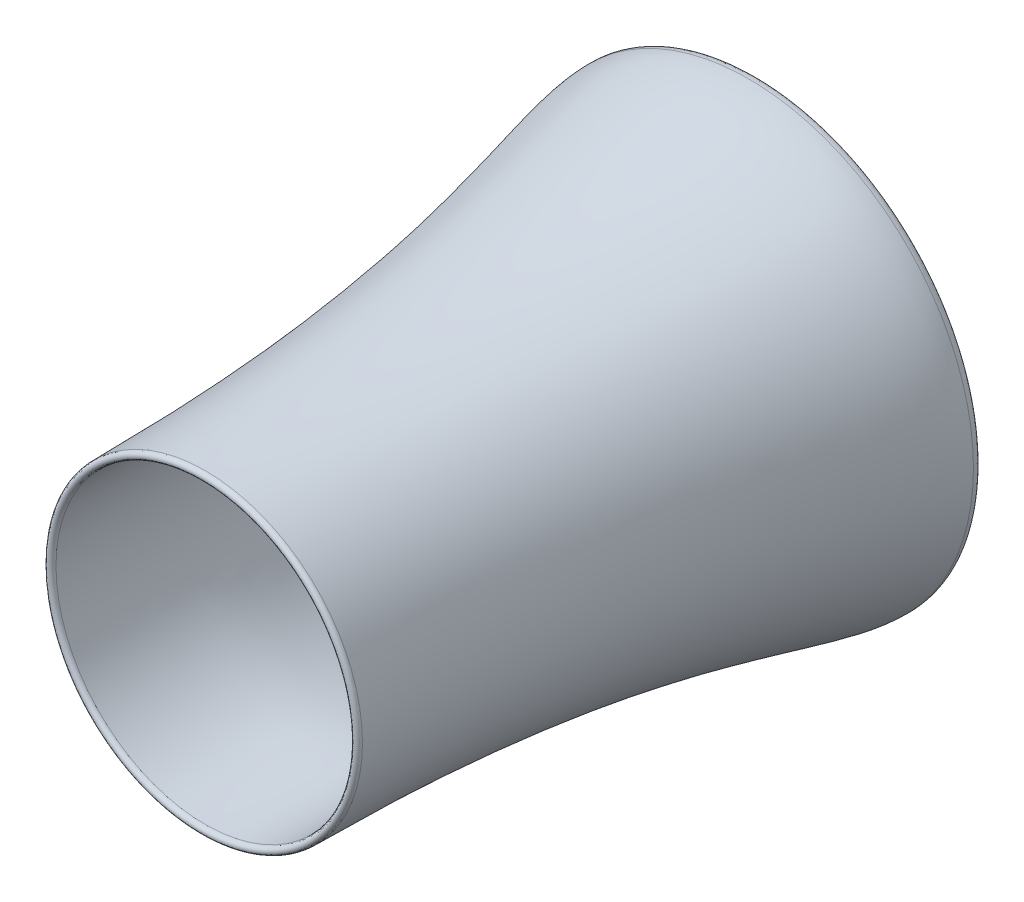
SolidWorks part; units mm, degrees
ref_plane "Front Plane" through (0, 0, 0) normal (0, 0, 1) x (1, 0, 0)
ref_plane "Top Plane" through (0, 0, 0) normal (0, 1, 0) x (1, 0, 0)
ref_plane "Right Plane" through (0, 0, 0) normal (1, 0, 0) x (0, 0, -1)
sketch "Sketch1" plane through (0, 0, 0) normal (0, 0, 1) x (1, 0, 0)
  circle A0 centre (0, 0) radius 50.8
  dimension "D1" = 101.6
ref_plane "Plane1" through (0, -254, 0) normal (0, 1, 0) x (1, 0, 0)
sketch "Sketch6" plane through (0, 0, 0) normal (0, 1, 0) x (1, 0, 0)
  line L0 (0, -99.6848) -> (0, 145.6048) construction
ref_plane "Plane2" through (0, -114.3, 0) normal (0, 1, 0) x (1, 0, 0)
sketch "Sketch12" plane through (0, 0, 0) normal (0, 1, 0) x (1, 0, 0)
  line L0 (0, -1104.7568) -> (0, -908.6135) construction
ref_plane "Plane3" through (0, 0, 203.2) normal (0, 0, 1) x (1, 0, 0)
ref_plane "Plane4" through (0, 0, 889) normal (0, 0, 1) x (1, 0, 0)
sketch "Sketch17" plane through (0, 0, 0) normal (0, 1, 0) x (1, 0, 0)
  line L0 (-259.4955, -43.5301) -> (-259.4955, 70.1436) construction
  line L1 (-110.6437, -1316.1124) -> (-110.6437, -853.5386) construction
  line L2 (-259.4955, 45.4622) -> (-387.328, 45.4622)
  line L3 (-387.328, 45.4622) -> (-387.328, -1084.8928)
  line L4 (-387.328, -1084.8928) -> (-110.6437, -1084.8928)
  spline S0 degree 3 poles (-259.4955, 45.4622) (-259.4955, -7.1736) (-207.7477, -105.8122) (-173.3147, -383.1384) (-92.4228, -818.9689) (-110.6437, -795.7842) (-110.6437, -1084.8928) knots 0 0 0 0 0.158009 0.206507 0.484977 1 1 1 1
sketch "Sketch21" plane through (0, 0, 0) normal (0, 1, 0) x (1, 0, 0)
  line L0 (-267.2369, -22.8536) -> (-267.2369, 113.778) construction
  line L1 (-126.7819, -1315.9117) -> (-126.7819, -853.874) construction
  line L2 (-259.4955, 45.4622) -> (-267.2369, 45.4622) construction
  line L3 (-110.6437, -1084.8928) -> (-126.7819, -1084.8928) construction
  line L4 (-110.6437, -1084.8928) -> (-126.7819, -1084.8928)
  line L6 (-259.4955, 45.4622) -> (-267.2369, 45.4622)
  spline S0 degree 3 poles (-259.4955, 45.4622) (-259.4955, -7.1736) (-207.7477, -105.8122) (-173.3147, -383.1384) (-92.4228, -818.9689) (-110.6437, -795.7842) (-110.6437, -1084.8928) knots 0 0 0 0 0.158009 0.206507 0.484977 1 1 1 1
  spline S1 degree 3 poles (-267.2369, 45.4622) (-267.2369, -79.9218) (-126.7819, -354.5837) (-126.7819, -1084.8928) knots 0 0 0 0 1 1 1 1
sketch "Sketch22" plane through (0, 0, 0) normal (0, 1, 0) x (1, 0, 0)
  line L0 (-267.2369, 45.4622) -> (-259.4955, 45.4622)
  line L1 (-259.4955, 41.6531) -> (-259.4955, 49.2713) construction
  line L2 (-267.2369, 46.8549) -> (-267.2369, 44.0695) construction
  spline S0 degree 3 poles (-267.2369, 45.4622) (-267.2369, 62.3955) (-259.4955, 62.3955) (-259.4955, 45.4622) knots 0 0 0 0 1 1 1 1
sketch "Sketch23" plane through (0, 0, 0) normal (0, 1, 0) x (1, 0, 0)
  line L0 (-126.7819, -1084.8928) -> (-110.6437, -1084.8928)
  line L1 (-126.7819, -1094.1039) -> (-126.7819, -1075.6818) construction
  line L2 (-110.6437, -1074.3198) -> (-110.6437, -1095.4658) construction
  spline S0 degree 3 poles (-126.7819, -1084.8928) (-126.7819, -1097.5928) (-110.6437, -1097.5928) (-110.6437, -1084.8928) knots 0 0 0 0 1 1 1 1
ref_plane "基准面1" through (200, 0, 0) normal (1, 0, 0) x (0, 0, -1)
ref_axis "基准轴1" through (200, 0, -115.7912) along (0, 0, 1)
revolve "旋转1" add sketch "Sketch21" angle 360 about axis through (200, 0, -115.7912) along (0, 0, 1)
revolve "旋转2" add sketch "Sketch22" angle 360 about axis through (200, 0, -115.7912) along (0, 0, 1)
revolve "旋转3" add sketch "Sketch23" angle 360 about axis through (200, 0, -115.7912) along (0, 0, 1)
